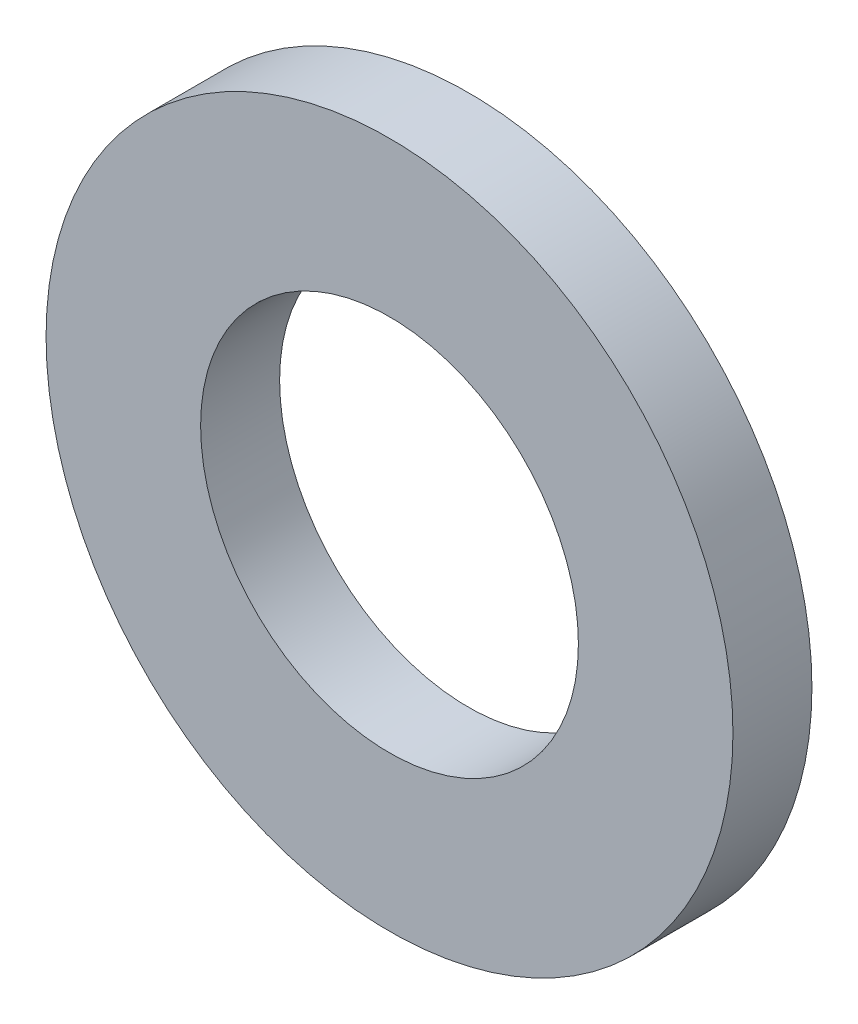
SolidWorks part; units mm, degrees
material "uhlíková ocel 7850"
ref_plane "Přední rovina" through (0, 0, 0) normal (0, 0, 1) x (1, 0, 0)
ref_plane "Horní rovina" through (0, 0, 0) normal (0, 1, 0) x (1, 0, 0)
ref_plane "Pravá rovina" through (0, 0, 0) normal (1, 0, 0) x (0, 0, -1)
sketch "Skica1" plane through (0, 0, 0) normal (0, 0, 1) x (1, 0, 0)
  circle A0 centre (0, 0) radius 10
  circle A1 centre (0, 0) radius 5.5
  dimension "D1" = 11
  dimension "D2" = 20
extrude "Přidat vysunutím1" add sketch "Skica1" along normal blind 2.3
